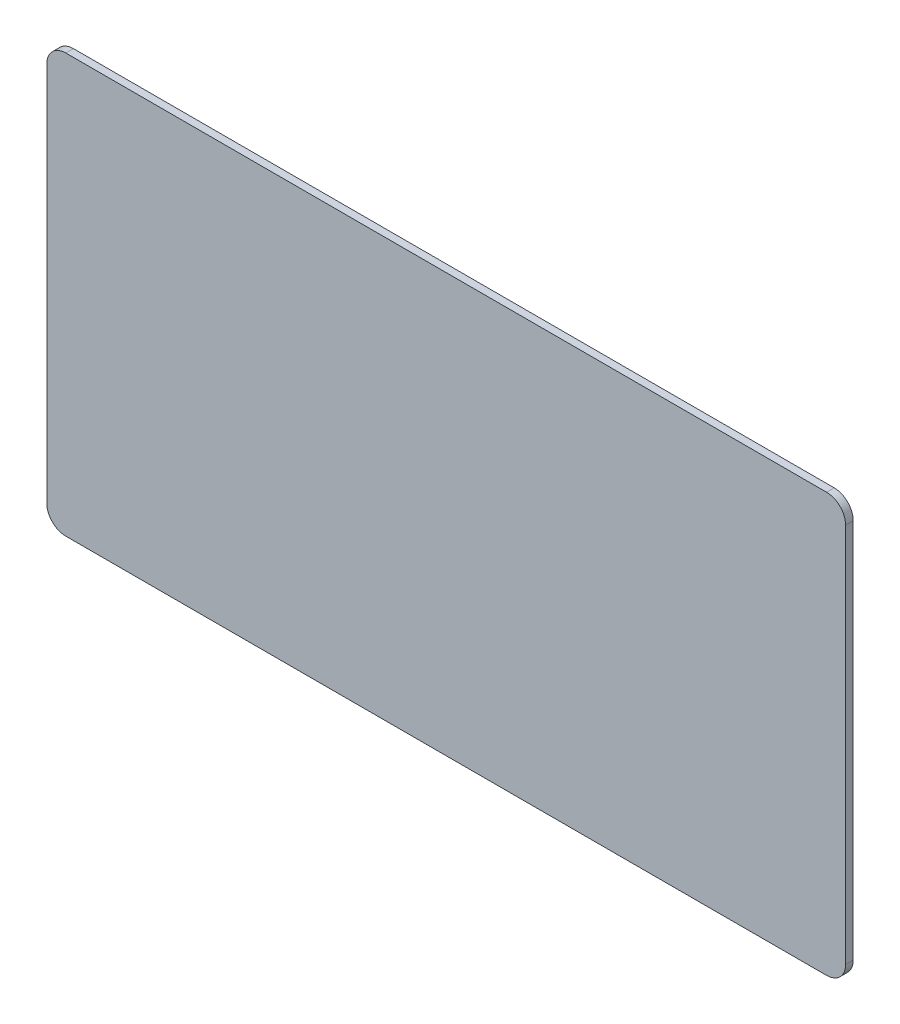
SolidWorks part; units mm, degrees
ref_plane "Front Plane" through (0, 0, 0) normal (0, 0, 1) x (1, 0, 0)
ref_plane "Top Plane" through (0, 0, 0) normal (0, 1, 0) x (1, 0, 0)
ref_plane "Right Plane" through (0, 0, 0) normal (1, 0, 0) x (0, 0, -1)
sketch "Sketch1" plane through (0, 0, 0) normal (0, 0, 1) x (1, 0, 0)
  line L1 (0, 0) -> (53.34, 0)
  line L2 (0, 0) -> (0, 27.94)
  line L3 (0, 27.94) -> (53.34, 27.94)
  line L4 (53.34, 0) -> (53.34, 27.94)
  dimension "D1" = 53.34
  dimension "D2" = 27.94
extrude "Extrude1" add sketch "Sketch1" along normal blind 0.508
ref_plane "Plane1" through (26.67, 0, 0) normal (-1, 0, 0) x (0, 0, 1)
ref_plane "Plane2" through (0, 13.97, 0) normal (0, -1, 0) x (1, 0, 0)
fillet "Fillet1" radius 1.27 4 edges at (53.34, 27.94, 0.254) (53.34, 0, 0.254) (0, 27.94, 0.254) (0, 0, 0.254)
